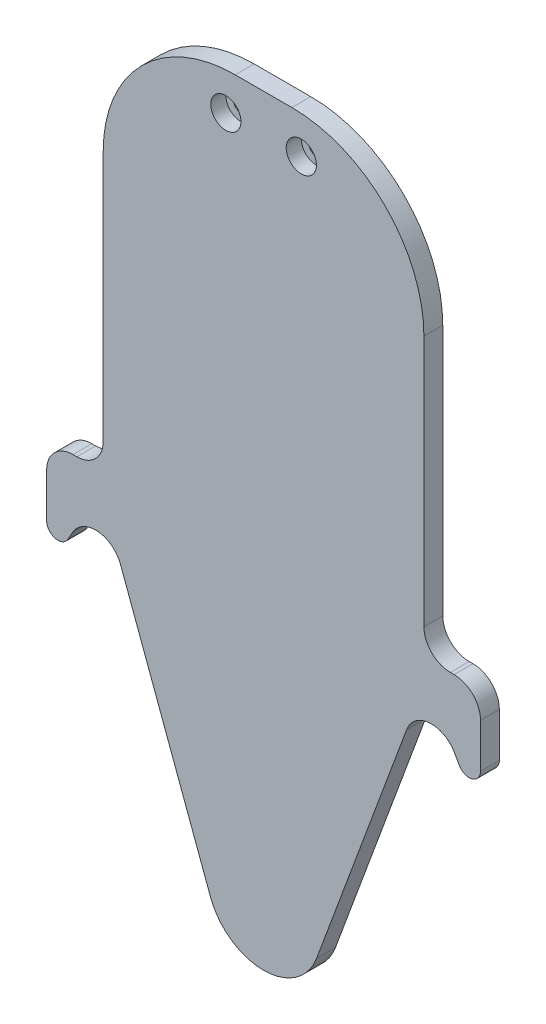
SolidWorks part; units mm, degrees
ref_plane "Płaszczyzna przednia" through (0, 0, 0) normal (0, 0, 1) x (1, 0, 0)
ref_plane "Płaszczyzna górna" through (0, 0, 0) normal (0, 1, 0) x (1, 0, 0)
ref_plane "Płaszczyzna prawa" through (0, 0, 0) normal (1, 0, 0) x (0, 0, -1)
sketch "Szkic1" plane through (0, 0, 0) normal (0, 0, 1) x (1, 0, 0)
  line L0 (-44.5, 0) -> (44.5, 0) construction
  line L1 (0, -61.7621) -> (0, 61.7621) construction
  line L2 (-37.9357, 2.4311) -> (-14.0663, -62.0192)
  line L3 (-11, 54) -> (11, 54) construction
  line L4 (-11, 54) -> (-11, -4) construction
  line L5 (-11, -4) -> (11, -4) construction
  line L6 (11, 54) -> (11, -4) construction
  line L7 (-11, 54) -> (11, -4) construction
  line L8 (-11, -4) -> (11, 54) construction
  line L9 (-27, 76) -> (27, 76) construction
  line L10 (-27, 76) -> (-27, -10) construction
  line L11 (-27, -10) -> (27, -10) construction
  line L12 (27, 76) -> (27, -10) construction
  line L13 (-27, 76) -> (27, -10) construction
  line L14 (-27, -10) -> (27, 76) construction
  line L15 (37.9357, 2.4311) -> (14.0663, -62.0192)
  line L16 (-50.5818, 3.4658) -> (-51.8935, 1.164)
  line L17 (50.5818, 3.4658) -> (51.8935, 1.164)
  line L18 (-57.5, 2.6494) -> (-57.5, 14.3259)
  line L19 (-50.5, 21.3259) -> (-49.5, 21.3259)
  line L20 (-42.5, 28.3259) -> (-42.5, 95)
  line L21 (-7.5, 130) -> (7.5, 130)
  line L22 (42.5, 95) -> (42.5, 28.3259)
  line L23 (49.5, 21.3259) -> (50.5, 21.3259)
  line L24 (57.5, 14.3259) -> (57.5, 2.6494)
  circle A0 centre (-44.5, 0) radius 7 construction
  circle A1 centre (44.5, 0) radius 7 construction
  circle A2 centre (0, 25) radius 22.5 construction
  arc A3 (-14.0663, -62.0192) -> (14.0663, -62.0192) centre (0, -56.8097) ccw
  arc A4 (37.9357, 2.4311) -> (50.5818, 3.4658) centre (44.5, 0) cw
  arc A5 (-50.5818, 3.4658) -> (-37.9357, 2.4311) centre (-44.5, 0) cw
  arc A6 (57.5, 2.6494) -> (51.8935, 1.164) centre (54.5, 2.6494) cw
  arc A7 (-57.5, 2.6494) -> (-51.8935, 1.164) centre (-54.5, 2.6494) ccw
  arc A8 (50.5, 21.3259) -> (57.5, 14.3259) centre (50.5, 14.3259) cw
  arc A9 (42.5, 28.3259) -> (49.5, 21.3259) centre (49.5, 28.3259) ccw
  arc A10 (-57.5, 14.3259) -> (-50.5, 21.3259) centre (-50.5, 14.3259) cw
  arc A11 (-49.5, 21.3259) -> (-42.5, 28.3259) centre (-49.5, 28.3259) ccw
  arc A12 (7.5, 130) -> (42.5, 95) centre (7.5, 95) cw
  arc A13 (-42.5, 95) -> (-7.5, 130) centre (-7.5, 95) cw
  point P8 (0, 25)
  point P14 (0, 33)
  point P27 (0, 130)
  point P30 (55.533, -5.2224)
  point P33 (0, -100)
  point P37 (-55.533, -5.2224)
  point P43 (57.5, -8.6741)
  point P46 (-57.5, -8.6741)
  point P49 (57.5, 21.3259)
  point P52 (42.5, 21.3259)
  point P55 (-57.5, 21.3259)
  point P58 (-42.5, 21.3259)
  dimension "D2" = 14
  dimension "D3" = 14
  dimension "D4" = 22
  dimension "D7" = 45
  dimension "D12" = 15
  dimension "D18" = 3
  dimension "D19" = 30
  dimension "D24" = 7
  dimension "D25" = 35
  dimension "D1" = 89
  dimension "D5" = 58
  dimension "D6" = 4
  dimension "D8" = 54
  dimension "D9" = 86
  dimension "D10" = 35
  dimension "D11" = 100
  dimension "D13" = 10
  dimension "D14" = 10
  dimension "D15" = 50
  dimension "D16" = 50
  dimension "D17" = 30
  dimension "D20" = 15
  dimension "D21" = 15
  dimension "D22" = 130
  dimension "D23" = 85
extrude "Dodanie-wyciągnięcie1" add sketch "Szkic1" along normal blind 5 contours A12 L22 A9 L23 A8 L24 A6 L17 A4 L15 A3 L2 A5 L16 A7 L18 A10 L19 A11 L20 A13 L21
sketch "Szkic2" plane through (0, 0, 0) normal (0, 0, -1) x (-1, 0, 0)
  line L1 (-27, 78) -> (27, 78)
  line L2 (-30, 75) -> (-30, -9)
  line L3 (-27, -12) -> (27, -12)
  line L4 (30, 75) -> (30, -9)
  line L5 (-30, 78) -> (30, -12) construction
  line L6 (-30, -12) -> (30, 78) construction
  arc A0 (-30, -9) -> (-27, -12) centre (-27, -9) ccw
  arc A1 (27, -12) -> (30, -9) centre (27, -9) ccw
  arc A2 (27, 78) -> (30, 75) centre (27, 75) cw
  arc A3 (-27, 78) -> (-30, 75) centre (-27, 75) ccw
  point P0 (0, 33)
  dimension "D3" = 3
  dimension "D1" = 60
  dimension "D2" = 90
extrude "Wytnij-wyciągnięcie1" cut sketch "Szkic2" against normal blind 1
sketch "Szkic3" plane through (0, 0, 0) normal (0, 0, -1) x (-1, 0, 0)
  line L0 (-61.395, 120) -> (61.395, 120) construction
  line L1 (7.5, 130) -> (-7.5, 130) construction
  circle A0 centre (-10, 120) radius 2
  circle A1 centre (10, 120) radius 2
  point P2 (0, 120)
  point P5 (0, 130)
  dimension "D2" = 4
  dimension "D3" = 4
  dimension "D1" = 10
  dimension "D4" = 10
  dimension "D5" = 10
extrude "Wytnij-wyciągnięcie2" cut sketch "Szkic3" against normal up to surface (5 mm away) up to face at (0, 23.8381, 5)
sketch "Szkic4" plane through (0, 0, 5) normal (0, 0, 1) x (1, 0, 0)
  circle A0 centre (-10, 120) radius 4
  circle A1 centre (10, 120) radius 4
  dimension "D1" = 8
  dimension "D2" = 8
extrude "Wytnij-wyciągnięcie3" cut sketch "Szkic4" against normal blind 4
sketch "Szkic5" plane through (0, 0, 0) normal (0, 0, -1) x (-1, 0, 0)
  circle A0 centre (-10, 120) radius 2
  circle A1 centre (10, 120) radius 2
  circle A2 centre (-10, 120) radius 5
  circle A3 centre (10, 120) radius 5
  dimension "D1" = 10
  dimension "D2" = 10
extrude "Dodanie-wyciągnięcie2" add sketch "Szkic5" along normal blind 5
fillet "Zaokrąglenie1" radius 2 4 edges at (5, 120, 0) (-15, 120, 0) (-15, 120, -5) (5, 120, -5)
